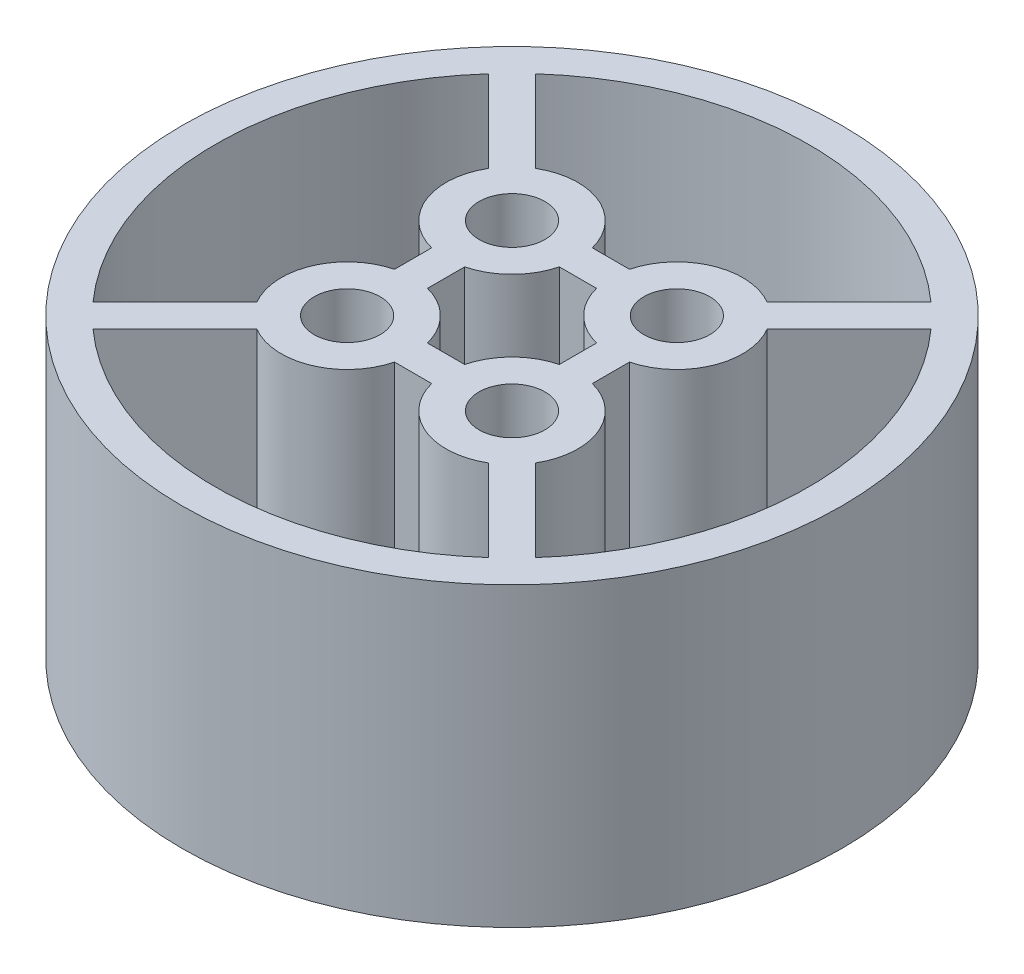
SolidWorks part; units mm, degrees
ref_plane "前视基准面" through (0, 0, 0) normal (0, 0, 1) x (1, 0, 0)
ref_plane "上视基准面" through (0, 0, 0) normal (0, 1, 0) x (1, 0, 0)
ref_plane "右视基准面" through (0, 0, 0) normal (1, 0, 0) x (0, 0, -1)
sketch "草图2" plane through (0, 0, 0) normal (0, 1, 0) x (1, 0, 0)
  line L0 (-20, 0) -> (26.5243, 0) construction
  line L2 (0, -20) -> (0, 31.4697) construction
  line L4 (-8.4457, 7.0315) -> (-13.4154, 12.0012)
  line L5 (-12.0012, 13.4154) -> (-7.0315, 8.4457)
  line L6 (0, 0) -> (-5, 5) construction
  line L7 (7.0315, 8.4457) -> (12.0012, 13.4154)
  line L8 (13.4154, 12.0012) -> (8.4457, 7.0315)
  line L9 (8.4457, -7.0315) -> (13.4154, -12.0012)
  line L10 (12.0012, -13.4154) -> (7.0315, -8.4457)
  line L11 (-7.0315, -8.4457) -> (-12.0012, -13.4154)
  line L12 (-13.4154, -12.0012) -> (-8.4457, -7.0315)
  line L13 (-1.127, 6) -> (1.127, 6)
  line L14 (-1.127, 4) -> (1.127, 4)
  line L17 (-5, 5) -> (5, 5) construction
  line L18 (6, 1.127) -> (6, -1.127)
  line L19 (4, 1.127) -> (4, -1.127)
  line L20 (1.127, -6) -> (-1.127, -6)
  line L21 (1.127, -4) -> (-1.127, -4)
  line L22 (-6, -1.127) -> (-6, 1.127)
  line L23 (-4, -1.127) -> (-4, 1.127)
  arc A1 (-8.4457, 7.0315) -> (-6, 1.127) centre (-5, 5) ccw
  circle A2 centre (0, 0) radius 20
  arc A3 (7.0315, 8.4457) -> (1.127, 6) centre (5, 5) ccw
  arc A4 (8.4457, -7.0315) -> (6, -1.127) centre (5, -5) ccw
  arc A5 (-7.0315, -8.4457) -> (-1.127, -6) centre (-5, -5) ccw
  arc A6 (-13.4154, 12.0012) -> (-13.4154, -12.0012) centre (0, 0) ccw
  arc A7 (-12.0012, -13.4154) -> (12.0012, -13.4154) centre (0, 0) ccw
  arc A8 (13.4154, -12.0012) -> (13.4154, 12.0012) centre (0, 0) ccw
  arc A9 (12.0012, 13.4154) -> (-12.0012, 13.4154) centre (0, 0) ccw
  arc A10 (-4, 1.127) -> (-1.127, 4) centre (-5, 5) ccw
  arc A11 (1.127, 4) -> (4, 1.127) centre (5, 5) ccw
  arc A12 (-6, -1.127) -> (-8.4457, -7.0315) centre (-5, -5) ccw
  arc A13 (1.127, -6) -> (7.0315, -8.4457) centre (5, -5) ccw
  arc A14 (4, -1.127) -> (1.127, -4) centre (5, -5) ccw
  arc A15 (6, 1.127) -> (8.4457, 7.0315) centre (5, 5) ccw
  arc A16 (-1.127, 6) -> (-7.0315, 8.4457) centre (-5, 5) ccw
  arc A17 (-1.127, -4) -> (-4, -1.127) centre (-5, -5) ccw
  circle A18 centre (-5, 5) radius 2
  circle A19 centre (5, 5) radius 2
  circle A20 centre (5, -5) radius 2
  circle A21 centre (-5, -5) radius 2
  point P36 (0, 0)
  point P38 (0, 0)
  point P49 (0, 0)
  point P56 (0, 0)
  dimension "D3" = 4
  dimension "D4" = 8
  dimension "D1" = 40
  dimension "D5" = 36
  dimension "D2" = 5
  dimension "D6" = 2
  dimension "D7" = 4
  dimension "D9" = 2
  dimension "D8" = 4
  dimension "D10" = 4
  dimension "D11" = 4
extrude "凸台-拉伸1" add sketch "草图2" along normal blind 18
